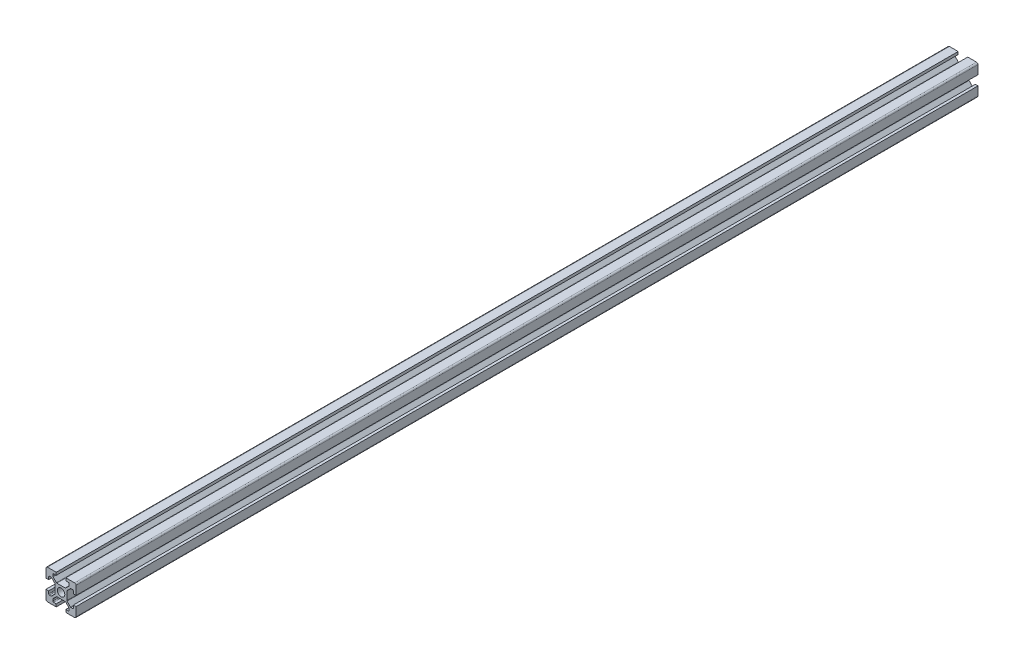
SolidWorks part; units mm, degrees
material "1060 Alloy"
ref_plane "Front Plane" through (0, 0, 0) normal (0, 0, 1) x (1, 0, 0)
ref_plane "Top Plane" through (0, 0, 0) normal (0, 1, 0) x (1, 0, 0)
ref_plane "Right Plane" through (0, 0, 0) normal (1, 0, 0) x (0, 0, -1)
sketch "Sketch1" plane through (0, 0, 0) normal (0, 0, 1) x (1, 0, 0)
  line L0 (20, 0) -> (-8.059, 28.059) construction
  line L1 (0, 0) -> (6.8, 0)
  line L2 (0, 0) -> (0, 6.8)
  line L3 (0, 20) -> (6.8, 20)
  line L4 (20, 0) -> (20, 6.8)
  line L5 (6.8, 20) -> (6.8, 18.2)
  line L6 (20, 20) -> (8.2322, 8.2322) construction
  line L7 (12.95, 6.1) -> (7.05, 6.1)
  line L8 (13.9, 7.05) -> (13.9, 12.95)
  line L9 (12.95, 13.9) -> (7.05, 13.9)
  line L10 (6.1, 7.05) -> (6.1, 12.95)
  line L11 (13.9, 6.1) -> (6.1, 13.9) construction
  line L12 (13.9, 13.9) -> (6.1, 6.1) construction
  line L13 (4.55, 16.4) -> (7.05, 13.9)
  line L14 (13.2, 18.2) -> (13.2, 20)
  line L15 (1.8, 6.8) -> (0, 6.8)
  line L16 (0, 13.2) -> (0, 20)
  line L17 (0, 13.2) -> (1.8, 13.2)
  line L18 (10, 10) -> (10, 13.9) construction
  line L19 (16.4, 4.55) -> (13.9, 7.05)
  line L20 (4.55, 16.4) -> (4.55, 18.2)
  line L21 (4.55, 18.2) -> (6.8, 18.2)
  line L22 (13.2, 18.2) -> (15.45, 18.2)
  line L23 (15.45, 18.2) -> (15.45, 16.4)
  line L24 (15.45, 16.4) -> (12.95, 13.9)
  line L25 (16.4, 4.55) -> (18.2, 4.55)
  line L26 (18.2, 4.55) -> (18.2, 6.8)
  line L27 (20, 6.8) -> (18.2, 6.8)
  line L28 (18.2, 13.2) -> (20, 13.2)
  line L29 (18.2, 13.2) -> (18.2, 15.45)
  line L30 (18.2, 15.45) -> (16.4, 15.45)
  line L31 (16.4, 15.45) -> (13.9, 12.95)
  line L32 (1.8, 4.55) -> (3.6, 4.55)
  line L33 (3.6, 15.45) -> (6.1, 12.95)
  line L34 (3.6, 15.45) -> (1.8, 15.45)
  line L35 (1.8, 15.45) -> (1.8, 13.2)
  line L36 (0, 13.2) -> (1.8, 13.2)
  line L37 (1.8, 6.8) -> (0, 6.8)
  line L38 (3.6, 4.55) -> (6.1, 7.05)
  line L39 (1.8, 6.8) -> (1.8, 4.55)
  line L40 (15.45, 3.6) -> (12.95, 6.1)
  line L41 (4.55, 3.6) -> (7.05, 6.1)
  line L42 (4.55, 1.8) -> (4.55, 3.6)
  line L43 (6.8, 1.8) -> (4.55, 1.8)
  line L44 (6.8, 1.8) -> (6.8, 0)
  line L45 (15.45, 3.6) -> (15.45, 1.8)
  line L46 (15.45, 1.8) -> (13.2, 1.8)
  line L47 (13.2, 0) -> (13.2, 1.8)
  line L48 (13.2, 20) -> (20, 20)
  line L49 (20, 13.2) -> (20, 20)
  line L50 (13.2, 0) -> (20, 0)
  line L51 (6.1, 6.1) -> (-5.5045, -5.5045) construction
  circle A0 centre (10, 10) radius 2.5
  point P25 (10, 16.4)
  point P39 (13.2, 19.1)
  point P46 (0.9, 6.8)
  dimension "D3" = 5
  dimension "D2" = 20
  dimension "D4" = 7.8
  dimension "D5" = 7.8
  dimension "D6" = 6.8
  dimension "D7" = 6.8
  dimension "D8" = 1.8
  dimension "D9" = 10.9
  dimension "D10" = 1.8
  dimension "D11" = 10.9
  dimension "D12" = 20
extrude "Boss-Extrude1" add sketch "Sketch1" along normal blind 300 contours L47 L50 L4 L27 L26 L25 L19 L8 L31 L30 L29 L28 L49 L48 L14 L22 L23 L24 L9 L13 L20 L21 L5 L3 L16 L17 L35 L34 L33 L10 L38 L32 L39 L15 L2 L1 L44 L43 L42 L41 L7 L40 L45 L46 A0
fillet "Fillet1" radius 1 4 edges at (20, 20, 150) (20, 0, 150) (0, 0, 150) (0, 20, 150)
fillet "Fillet2" radius 0.5 6 edges at (4.55, 18.2, 150) (4.55, 16.4, 150) (7.05, 13.9, 150) (15.45, 18.2, 150) (15.45, 16.4, 150) (12.95, 13.9, 150)
fillet "Fillet3" radius 0.5 6 edges at (18.2, 15.45, 150) (16.4, 15.45, 150) (13.9, 12.95, 150) (18.2, 4.55, 150) (13.9, 7.05, 150) (16.4, 4.55, 150)
fillet "Fillet4" radius 0.5 6 edges at (1.8, 15.45, 150) (3.6, 15.45, 150) (6.1, 12.95, 150) (3.6, 4.55, 150) (1.8, 4.55, 150) (6.1, 7.05, 150)
fillet "Fillet5" radius 0.5 6 edges at (7.05, 6.1, 150) (4.55, 3.6, 150) (4.55, 1.8, 150) (15.45, 1.8, 150) (15.45, 3.6, 150) (12.95, 6.1, 150)
sketch "Sketch4" plane through (0, 0, 0) normal (0, 0, -1) x (-1, 0, 0)
  line L44 (-13.2, 20) -> (-19, 20)
  line L45 (-20, 19) -> (-20, 13.2)
  line L46 (-20, 13.2) -> (-18.2, 13.2)
  line L47 (-18.2, 13.2) -> (-18.2, 14.95)
  line L48 (-17.7, 15.45) -> (-16.6071, 15.45)
  line L49 (-16.2536, 15.3036) -> (-14.0464, 13.0964)
  line L50 (-13.9, 12.7429) -> (-13.9, 7.2571)
  line L51 (-14.0464, 6.9036) -> (-16.2536, 4.6964)
  line L52 (-16.6071, 4.55) -> (-17.7, 4.55)
  line L53 (-18.2, 5.05) -> (-18.2, 6.8)
  line L54 (-18.2, 6.8) -> (-20, 6.8)
  line L55 (-20, 6.8) -> (-20, 1)
  line L56 (-19, 0) -> (-13.2, 0)
  line L57 (-13.2, 0) -> (-13.2, 1.8)
  line L58 (-13.2, 1.8) -> (-14.95, 1.8)
  line L59 (-15.45, 2.3) -> (-15.45, 3.3929)
  line L60 (-15.3036, 3.7464) -> (-13.0964, 5.9536)
  line L61 (-12.7429, 6.1) -> (-7.2571, 6.1)
  line L62 (-6.9036, 5.9536) -> (-4.6964, 3.7464)
  line L63 (-4.55, 3.3929) -> (-4.55, 2.3)
  line L64 (-5.05, 1.8) -> (-6.8, 1.8)
  line L65 (-6.8, 1.8) -> (-6.8, 0)
  line L66 (-6.8, 0) -> (-1, 0)
  line L67 (0, 1) -> (0, 6.8)
  line L68 (0, 6.8) -> (-1.8, 6.8)
  line L69 (-1.8, 6.8) -> (-1.8, 5.05)
  line L70 (-2.3, 4.55) -> (-3.3929, 4.55)
  line L71 (-3.7464, 4.6964) -> (-5.9536, 6.9036)
  line L72 (-6.1, 7.2571) -> (-6.1, 12.7429)
  line L73 (-5.9536, 13.0964) -> (-3.7464, 15.3036)
  line L74 (-3.3929, 15.45) -> (-2.3, 15.45)
  line L75 (-1.8, 14.95) -> (-1.8, 13.2)
  line L76 (-1.8, 13.2) -> (0, 13.2)
  line L77 (0, 13.2) -> (0, 19)
  line L78 (-1, 20) -> (-6.8, 20)
  line L79 (-6.8, 20) -> (-6.8, 18.2)
  line L80 (-6.8, 18.2) -> (-5.05, 18.2)
  line L81 (-4.55, 17.7) -> (-4.55, 16.6071)
  line L82 (-4.6964, 16.2536) -> (-6.9036, 14.0464)
  line L83 (-7.2571, 13.9) -> (-12.7429, 13.9)
  line L84 (-13.0964, 14.0464) -> (-15.3036, 16.2536)
  line L85 (-15.45, 16.6071) -> (-15.45, 17.7)
  line L86 (-14.95, 18.2) -> (-13.2, 18.2)
  line L87 (-13.2, 18.2) -> (-13.2, 20)
  line L88 (-13.2, 20) -> (-19, 20)
  line L89 (-20, 19) -> (-20, 13.2)
  line L90 (-20, 13.2) -> (-18.2, 13.2)
  line L91 (-18.2, 13.2) -> (-18.2, 14.95)
  line L92 (-17.7, 15.45) -> (-16.6071, 15.45)
  line L93 (-16.2536, 15.3036) -> (-14.0464, 13.0964)
  line L94 (-13.9, 12.7429) -> (-13.9, 7.2571)
  line L95 (-14.0464, 6.9036) -> (-16.2536, 4.6964)
  line L96 (-16.6071, 4.55) -> (-17.7, 4.55)
  line L97 (-18.2, 5.05) -> (-18.2, 6.8)
  line L98 (-18.2, 6.8) -> (-20, 6.8)
  line L99 (-20, 6.8) -> (-20, 1)
  line L100 (-19, 0) -> (-13.2, 0)
  line L101 (-13.2, 0) -> (-13.2, 1.8)
  line L102 (-13.2, 1.8) -> (-14.95, 1.8)
  line L103 (-15.45, 2.3) -> (-15.45, 3.3929)
  line L104 (-15.3036, 3.7464) -> (-13.0964, 5.9536)
  line L105 (-12.7429, 6.1) -> (-7.2571, 6.1)
  line L106 (-6.9036, 5.9536) -> (-4.6964, 3.7464)
  line L107 (-4.55, 3.3929) -> (-4.55, 2.3)
  line L108 (-5.05, 1.8) -> (-6.8, 1.8)
  line L109 (-6.8, 1.8) -> (-6.8, 0)
  line L110 (-6.8, 0) -> (-1, 0)
  line L111 (0, 1) -> (0, 6.8)
  line L112 (0, 6.8) -> (-1.8, 6.8)
  line L113 (-1.8, 6.8) -> (-1.8, 5.05)
  line L114 (-2.3, 4.55) -> (-3.3929, 4.55)
  line L115 (-3.7464, 4.6964) -> (-5.9536, 6.9036)
  line L116 (-6.1, 7.2571) -> (-6.1, 12.7429)
  line L117 (-5.9536, 13.0964) -> (-3.7464, 15.3036)
  line L118 (-3.3929, 15.45) -> (-2.3, 15.45)
  line L119 (-1.8, 14.95) -> (-1.8, 13.2)
  line L120 (-1.8, 13.2) -> (0, 13.2)
  line L121 (0, 13.2) -> (0, 19)
  line L122 (-1, 20) -> (-6.8, 20)
  line L123 (-6.8, 20) -> (-6.8, 18.2)
  line L124 (-6.8, 18.2) -> (-5.05, 18.2)
  line L125 (-4.55, 17.7) -> (-4.55, 16.6071)
  line L126 (-4.6964, 16.2536) -> (-6.9036, 14.0464)
  line L127 (-7.2571, 13.9) -> (-12.7429, 13.9)
  line L128 (-13.0964, 14.0464) -> (-15.3036, 16.2536)
  line L129 (-15.45, 16.6071) -> (-15.45, 17.7)
  line L130 (-14.95, 18.2) -> (-13.2, 18.2)
  line L131 (-13.2, 18.2) -> (-13.2, 20)
  arc A28 (-19, 20) -> (-20, 19) centre (-19, 19) ccw
  arc A29 (-17.7, 15.45) -> (-18.2, 14.95) centre (-17.7, 14.95) ccw
  arc A30 (-16.2536, 15.3036) -> (-16.6071, 15.45) centre (-16.6071, 14.95) ccw
  arc A31 (-13.9, 12.7429) -> (-14.0464, 13.0964) centre (-14.4, 12.7429) ccw
  arc A32 (-14.0464, 6.9036) -> (-13.9, 7.2571) centre (-14.4, 7.2571) ccw
  arc A33 (-16.6071, 4.55) -> (-16.2536, 4.6964) centre (-16.6071, 5.05) ccw
  arc A34 (-18.2, 5.05) -> (-17.7, 4.55) centre (-17.7, 5.05) ccw
  arc A35 (-20, 1) -> (-19, 0) centre (-19, 1) ccw
  arc A36 (-15.45, 2.3) -> (-14.95, 1.8) centre (-14.95, 2.3) ccw
  arc A37 (-15.3036, 3.7464) -> (-15.45, 3.3929) centre (-14.95, 3.3929) ccw
  arc A38 (-12.7429, 6.1) -> (-13.0964, 5.9536) centre (-12.7429, 5.6) ccw
  arc A39 (-6.9036, 5.9536) -> (-7.2571, 6.1) centre (-7.2571, 5.6) ccw
  arc A40 (-4.55, 3.3929) -> (-4.6964, 3.7464) centre (-5.05, 3.3929) ccw
  arc A41 (-5.05, 1.8) -> (-4.55, 2.3) centre (-5.05, 2.3) ccw
  arc A42 (-1, 0) -> (0, 1) centre (-1, 1) ccw
  arc A43 (-2.3, 4.55) -> (-1.8, 5.05) centre (-2.3, 5.05) ccw
  arc A44 (-3.7464, 4.6964) -> (-3.3929, 4.55) centre (-3.3929, 5.05) ccw
  arc A45 (-6.1, 7.2571) -> (-5.9536, 6.9036) centre (-5.6, 7.2571) ccw
  arc A46 (-5.9536, 13.0964) -> (-6.1, 12.7429) centre (-5.6, 12.7429) ccw
  arc A47 (-3.3929, 15.45) -> (-3.7464, 15.3036) centre (-3.3929, 14.95) ccw
  arc A48 (-1.8, 14.95) -> (-2.3, 15.45) centre (-2.3, 14.95) ccw
  arc A49 (0, 19) -> (-1, 20) centre (-1, 19) ccw
  arc A50 (-4.55, 17.7) -> (-5.05, 18.2) centre (-5.05, 17.7) ccw
  arc A51 (-4.6964, 16.2536) -> (-4.55, 16.6071) centre (-5.05, 16.6071) ccw
  arc A52 (-7.2571, 13.9) -> (-6.9036, 14.0464) centre (-7.2571, 14.4) ccw
  arc A53 (-13.0964, 14.0464) -> (-12.7429, 13.9) centre (-12.7429, 14.4) ccw
  arc A54 (-15.45, 16.6071) -> (-15.3036, 16.2536) centre (-14.95, 16.6071) ccw
  arc A55 (-14.95, 18.2) -> (-15.45, 17.7) centre (-14.95, 17.7) ccw
  arc A56 (-19, 20) -> (-20, 19) centre (-19, 19) ccw
  arc A57 (-17.7, 15.45) -> (-18.2, 14.95) centre (-17.7, 14.95) ccw
  arc A58 (-16.2536, 15.3036) -> (-16.6071, 15.45) centre (-16.6071, 14.95) ccw
  arc A59 (-13.9, 12.7429) -> (-14.0464, 13.0964) centre (-14.4, 12.7429) ccw
  arc A60 (-14.0464, 6.9036) -> (-13.9, 7.2571) centre (-14.4, 7.2571) ccw
  arc A61 (-16.6071, 4.55) -> (-16.2536, 4.6964) centre (-16.6071, 5.05) ccw
  arc A62 (-18.2, 5.05) -> (-17.7, 4.55) centre (-17.7, 5.05) ccw
  arc A63 (-20, 1) -> (-19, 0) centre (-19, 1) ccw
  arc A64 (-15.45, 2.3) -> (-14.95, 1.8) centre (-14.95, 2.3) ccw
  arc A65 (-15.3036, 3.7464) -> (-15.45, 3.3929) centre (-14.95, 3.3929) ccw
  arc A66 (-12.7429, 6.1) -> (-13.0964, 5.9536) centre (-12.7429, 5.6) ccw
  arc A67 (-6.9036, 5.9536) -> (-7.2571, 6.1) centre (-7.2571, 5.6) ccw
  arc A68 (-4.55, 3.3929) -> (-4.6964, 3.7464) centre (-5.05, 3.3929) ccw
  arc A69 (-5.05, 1.8) -> (-4.55, 2.3) centre (-5.05, 2.3) ccw
  arc A70 (-1, 0) -> (0, 1) centre (-1, 1) ccw
  arc A71 (-2.3, 4.55) -> (-1.8, 5.05) centre (-2.3, 5.05) ccw
  arc A72 (-3.7464, 4.6964) -> (-3.3929, 4.55) centre (-3.3929, 5.05) ccw
  arc A73 (-6.1, 7.2571) -> (-5.9536, 6.9036) centre (-5.6, 7.2571) ccw
  arc A74 (-5.9536, 13.0964) -> (-6.1, 12.7429) centre (-5.6, 12.7429) ccw
  arc A75 (-3.3929, 15.45) -> (-3.7464, 15.3036) centre (-3.3929, 14.95) ccw
  arc A76 (-1.8, 14.95) -> (-2.3, 15.45) centre (-2.3, 14.95) ccw
  arc A77 (0, 19) -> (-1, 20) centre (-1, 19) ccw
  arc A78 (-4.55, 17.7) -> (-5.05, 18.2) centre (-5.05, 17.7) ccw
  arc A79 (-4.6964, 16.2536) -> (-4.55, 16.6071) centre (-5.05, 16.6071) ccw
  arc A80 (-7.2571, 13.9) -> (-6.9036, 14.0464) centre (-7.2571, 14.4) ccw
  arc A81 (-13.0964, 14.0464) -> (-12.7429, 13.9) centre (-12.7429, 14.4) ccw
  arc A82 (-15.45, 16.6071) -> (-15.3036, 16.2536) centre (-14.95, 16.6071) ccw
  arc A83 (-14.95, 18.2) -> (-15.45, 17.7) centre (-14.95, 17.7) ccw
  dimension "D1" = 0
extrude "Boss-Extrude2" add sketch "Sketch4" along normal blind 300
